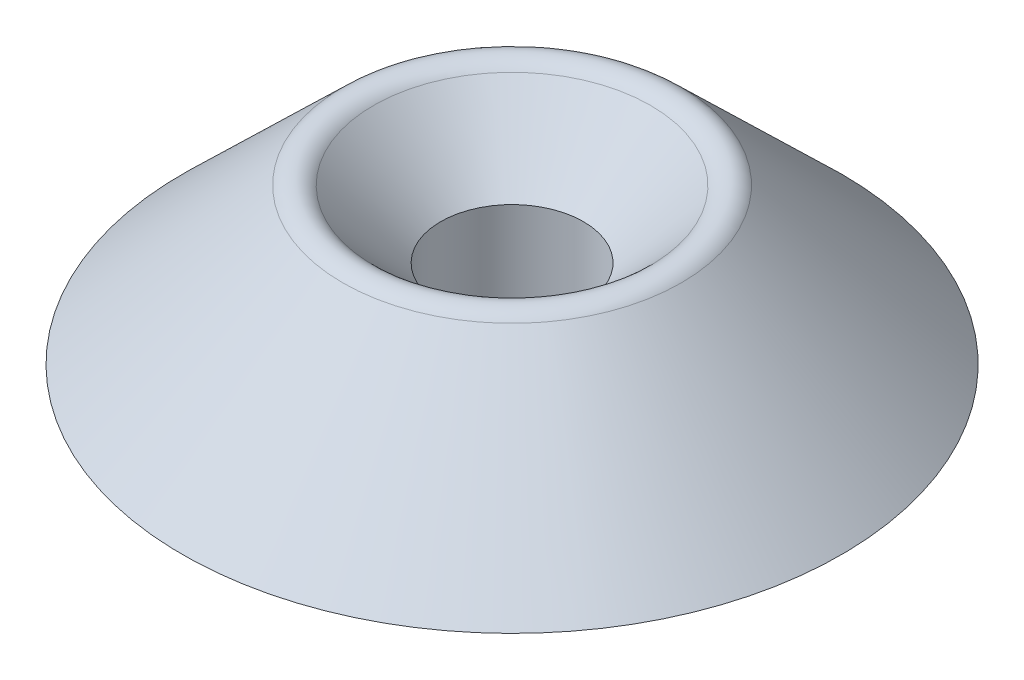
SolidWorks part; units mm, degrees
ref_plane "Plan de face" through (0, 0, 0) normal (0, 0, 1) x (1, 0, 0)
ref_plane "Plan de dessus" through (0, 0, 0) normal (0, 1, 0) x (1, 0, 0)
ref_plane "Plan de droite" through (0, 0, 0) normal (1, 0, 0) x (0, 0, -1)
sketch "Esquisse1" plane through (0, 0, 0) normal (0, 0, 1) x (1, 0, 0)
  line L0 (3.25, 0) -> (15, 0)
  line L1 (15, 0) -> (7, 7.75)
  line L2 (7, 7.75) -> (3.25, 4)
  line L3 (3.25, 4) -> (3.25, 0)
  line L4 (0, 0) -> (0, 6.2665) construction
  dimension "D1" = 3.25
  dimension "D2" = 7
  dimension "D3" = 135
  dimension "D4" = 4
  dimension "D5" = 15
revolve "Révolution1" add sketch "Esquisse1" angle 360 about L4
fillet "Congé1" radius 1 1 edges at (0, 7.75, -7)
